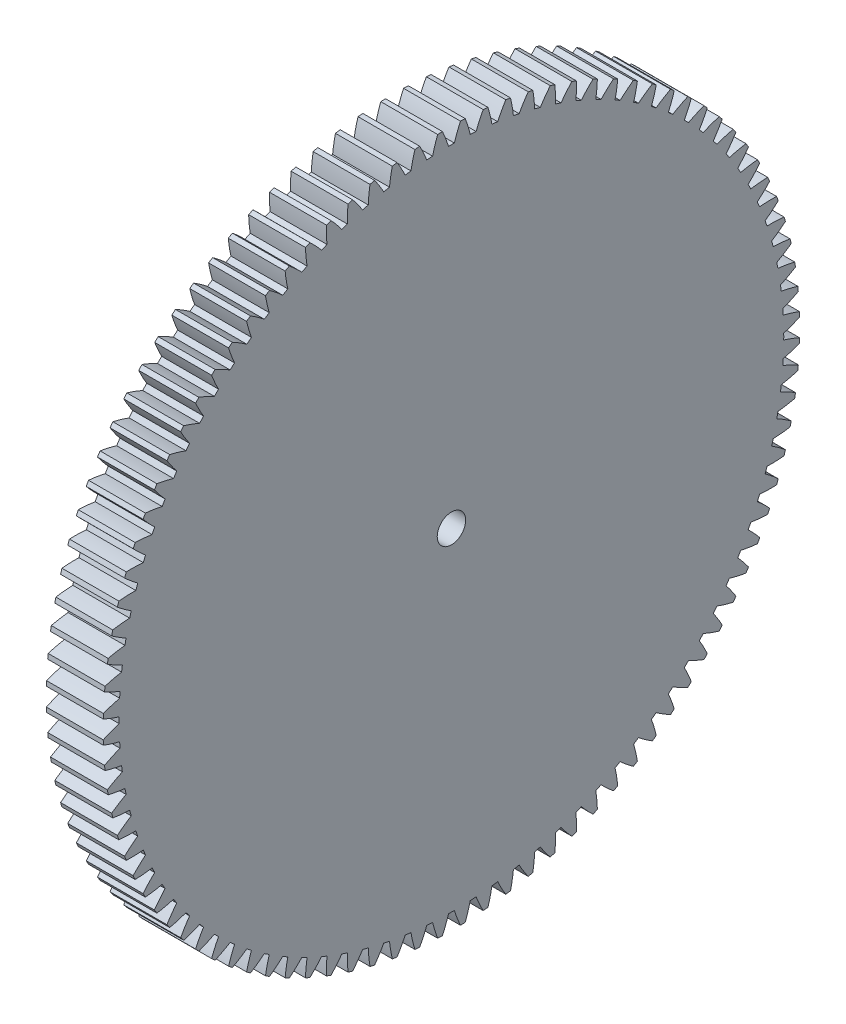
SolidWorks part; units mm, degrees
ref_plane "Plane1" through (0, 0, 0) normal (0, 0, 1) x (1, 0, 0)
ref_plane "Plane2" through (0, 0, 0) normal (0, 1, 0) x (1, 0, 0)
ref_plane "Plane3" through (0, 0, 0) normal (1, 0, 0) x (0, 0, -1)
sketch "HoldingSke" plane through (0, 0, 0) normal (0, 1, 0) x (1, 0, 0)
  line L0 (0, 0) -> (-0.0836, -0.7956)
  line L1 (-15, 0) -> (100, 0) construction
  line L2 (0, 0) -> (-2.1039, 2.3779)
  line L3 (0, 0) -> (-11.863, 4.5341)
  line L4 (0, 0) -> (-0.9027, 8.5887)
  line L5 (0, 0) -> (-46.8476, -17.4728)
  line L6 (0, 0) -> (-8.2896, -5.593)
  line L7 (-2.1039, 2.3779) -> (8.6586, 51.2059)
  line L8 (-76.2, 54.61) -> (-75.3, 54.61)
  line L9 (-71.009, 38.7566) -> (-53.1078, 45.2721)
  line L10 (-76.2, 71.12) -> (104.1128, 71.12)
  line L11 (0, 0) -> (-10, 0)
  line L12 (-76.2, 101.6) -> (-76.155, 101.6)
  line L13 (24.9733, 27.94) -> (52.9518, 28.4284)
  line L14 (24.9733, 27.94) -> (24.9743, 27.94)
  line L15 (24.9733, 27.94) -> (100.4006, 29.5858)
  line L16 (-63.627, -1.25) -> (-12.827, -1.25)
  circle A0 centre (0, 0) radius 2.5
  circle A1 centre (0, 0) radius 37.5
  circle A2 centre (0, 0) radius 37.5
  circle A3 centre (0, 0) radius 2.5
  dimension "MHD" = 75
  dimension "Hub_dia" = 75
  dimension "Bore" = 5
  dimension "MBD" = 5
  dimension "Num_teeth" = 96
  dimension "Pitch" = 0.8
  dimension "Overall_len" = 50
  dimension "Show_teeth" = 96
  dimension "Thickness" = 10
  dimension "OAL" = 50.0001
  dimension "T_dim" = 0.9
  dimension "Ap" = 20
  dimension "H" = 19.05
  dimension "Pitch_radius" = 180.3128
  dimension "Width" = 10
  dimension "Backlash" = 0.045
  dimension "Addendum_fac" = 1
  dimension "Dedendum_fac" = 1.25
  dimension "Clearance_fac" = 0.25
  dimension "Dedendum_add" = 0.001
  dimension "Module" = 1.25
sketch "BasProSke" plane through (0, 0, 0) normal (0, 1, 0) x (1, 0, 0)
  line L0 (-10, 0) -> (60, 0) construction
  line L1 (0, 0) -> (0, 61.25)
  line L2 (0, 0) -> (10, 0)
  line L3 (10, 0) -> (10, 61.25)
  line L4 (10, 61.25) -> (0, 61.25)
  dimension "Thickness" = 10
  dimension "Diameter" = 122.5
revolve "Base-Revolve" add sketch "BasProSke" angle 360 about L0
sketch "TooCutSke" plane through (0, 0, 0) normal (1, 0, 0) x (0, 0, -1)
  line L1 (0, 0) -> (0, 107) construction
  line L2 (0, 0) -> (-1.0605, 59.9906) construction
  line L3 (0, 0) -> (-3.9258, 119.9222) construction
  line L4 (-1.0605, 59.9906) -> (-1.9629, 59.9611) construction
  arc A0 (0.5154, 58.4342) -> (-0.5154, 58.4342) centre (0, 0) ccw
  arc A1 (1.5946, 61.2546) -> (-1.5946, 61.2546) centre (0, 0) ccw
  circle A2 centre (0, 0) radius 60 construction
  circle A3 centre (0, 0) radius 56.3816 construction
  arc A4 (-0.5154, 58.4342) -> (-1.5946, 61.2546) centre (-23.4257, 51.2846) ccw
  arc A5 (1.5946, 61.2546) -> (0.5154, 58.4342) centre (23.4257, 51.2846) ccw
  dimension "Root_dia" = 116.873
  dimension "Overcut_dia" = 122.5508
  dimension "Pitch_dia" = 120
  dimension "Base_dia" = 112.7631
  dimension "Flank_rad" = 24
  dimension "Half_ang" = 1.875
  dimension "Half_CT" = 0.903
extrude "ToothCut" cut sketch "TooCutSke" along normal through all
fillet "Breaks" [suppressed] radius 0.025
fillet "RootFillets" [suppressed] radius 0.3135
pattern_circular "TeethCuts" count 96 every 3.75 about axis through (-10, 0, 0) along (1, 0, 0) of "ToothCut", "RootFillets", "Breaks"
sketch "HubNeaOneSke" plane through (0, 0, 0) normal (-1, 0, 0) x (0, 0, 1)
  circle A0 centre (0, 0) radius 37.5
  dimension "Diameter" = 75
extrude "HubNearOne" [suppressed] add sketch "HubNeaOneSke" along normal blind 40.0001
sketch "HubNeaBotSke" plane through (0, 0, 0) normal (-1, 0, 0) x (0, 0, 1)
  circle A0 centre (0, 0) radius 37.5
  dimension "Diameter" = 75
extrude "HubNearBoth" [suppressed] add sketch "HubNeaBotSke" along normal blind 20
ref_plane "FarPln" through (10, 0, 0) normal (1, 0, 0) x (0, 0, -1)
sketch "HubFarSke" plane through (10, 0, 0) normal (1, 0, 0) x (0, 0, -1)
  circle A0 centre (0, 0) radius 37.5
  dimension "Diameter" = 75
extrude "HubFar" [suppressed] add sketch "HubFarSke" along normal blind 20
sketch "BorSke" plane through (0, 0, 0) normal (1, 0, 0) x (0, 0, -1)
  circle A0 centre (0, 0) radius 2.5
  dimension "Diameter" = 5
extrude "Bore" cut sketch "BorSke" along normal mid plane 100.0001
sketch "KeySke" plane through (0, 0, 0) normal (1, 0, 0) x (0, 0, -1)
  line L0 (-1, 0) -> (-1, 3.4)
  line L1 (-1, 3.4) -> (1, 3.4)
  line L2 (1, 3.4) -> (1, 0)
  line L3 (0, 0) -> (0, 34) construction
  line L4 (-1, 0) -> (1, 0)
  dimension "Offset" = 3.4
  dimension "Width" = 2
extrude "Keyway" [suppressed] cut sketch "KeySke" along normal mid plane 100.0001
pattern_circular "Keyway2" [suppressed] count 2 every 90 about axis through (-10, 0, 0) along (1, 0, 0)
equation "' \"Module@HoldingSke\" = 6.35"
equation "' \"Num_teeth@HoldingSke\" = 12"
equation "' \"Ap@HoldingSke\" =  20"
equation "' \"Ap@HoldingSke\" = 20"
equation "' \"Width@HoldingSke\" = 0.5 * 25.4"
equation "' \"Hub_dia@HoldingSke\"= 1 * 25.4"
equation "' \"Hub_dia@HoldingSke\" = 1 * 25.4"
equation "' \"Overall_len@HoldingSke\" = 1.0 * 25.4"
equation "' \"Bore@HoldingSke\" = 0.75 * 25.4"
equation "' \"T_dim@HoldingSke\" = 0.1 * 25.4"
equation "' \"Width@KeySke\" = 0.25 * 25.4"
equation "' \"Show_teeth@HoldingSke\" = 13"
equation "' \"Backlash@HoldingSke\" = 0.009 * 25.4"
equation "' \"Addendum_fac@HoldingSke\" = 1.0"
equation "' \"Dedendum_fac@HoldingSke\" = 1.25"
equation "' \"Dedendum_add@HoldingSke\" = 0.00005 * 25.4"
equation "' \"Clearance_fac@HoldingSke\" = 0.25"
equation "\"Pitch@HoldingSke\" = 1 / \"Module@HoldingSke\""
equation "\"Overcut_dia@TooCutSke\" = (\"Num_teeth@HoldingSke\" + 2 * \"Addendum_fac@HoldingSke\") / \"Pitch@HoldingSke\" + 0.002 * 25.4"
equation "\"Pitch_dia@TooCutSke\" = \"Num_teeth@HoldingSke\" / \"Pitch@HoldingSke\""
equation "\"Base_dia@TooCutSke\" = \"Num_teeth@HoldingSke\" / \"Pitch@HoldingSke\" * cos((\"Ap@HoldingSke\"  * 3.14159265 / 180))"
equation "\"Root_dia@TooCutSke\" = (\"Num_teeth@HoldingSke\" + 2) / \"Pitch@HoldingSke\" - 2 * (\"Addendum_fac@HoldingSke\" + \"Dedendum_fac@HoldingSke\") / \"Pitch@HoldingSke\" - \"Dedendum_add@HoldingSke\" * 2"
equation "\"Half_ang@TooCutSke\" = 180 / \"Num_teeth@HoldingSke\""
equation "\"Half_CT@TooCutSke\" = \"Num_teeth@HoldingSke\" / \"Pitch@HoldingSke\" * sin((3.14159265 / 2 / \"Num_teeth@HoldingSke\")) / 2 - 7 * \"Backlash@HoldingSke\" / 4"
equation "\"Flank_rad@TooCutSke\" = \"Num_teeth@HoldingSke\" / \"Pitch@HoldingSke\" / 5"
equation "\"Radius@RootFillets\" = \"Clearance_fac@HoldingSke\" / \"Pitch@HoldingSke\" + \"Dedendum_add@HoldingSke\""
equation "\"Break_rad@Breaks\" = 0.02 / \"Pitch@HoldingSke\""
equation "\"Thickness@HoldingSke\" = \"Width@HoldingSke\""
equation "\"OAL@HoldingSke\" = \"Thickness@HoldingSke\""
equation "\"MHD@HoldingSke\" = (\"Num_teeth@HoldingSke\" + 2) / \"Pitch@HoldingSke\" - 2 * (\"Addendum_fac@HoldingSke\" + \"Dedendum_fac@HoldingSke\")  / \"Pitch@HoldingSke\" - \"Dedendum_add@HoldingSke\" * 2"
equation "\"MBD@HoldingSke\" = (\"Num_teeth@HoldingSke\" + 2) / \"Pitch@HoldingSke\" - 2 * (\"Addendum_fac@HoldingSke\" + \"Dedendum_fac@HoldingSke\")  / \"Pitch@HoldingSke\" - \"Dedendum_add@HoldingSke\" * 2 - 0.002 * 25.4"
equation "\"MHD@HoldingSke\" = ((sgn( \"MHD@HoldingSke\" - \"Hub_dia@HoldingSke\" )-1)*( \"MHD@HoldingSke\" - \"Hub_dia@HoldingSke\" ))/-2+ \"Hub_dia@HoldingSke\""
equation "\"MBD@HoldingSke\" = ((sgn( \"MBD@HoldingSke\" - \"Bore@HoldingSke\" )-1)*( \"MBD@HoldingSke\" - \"Bore@HoldingSke\" ))/-2+ \"Bore@HoldingSke\""
equation "\"OAL@HoldingSke\" = ((sgn( \"OAL@HoldingSke\" - \"Overall_len@HoldingSke\" )+1)*( \"OAL@HoldingSke\" - \"Overall_len@HoldingSke\" ))/2 + \"Overall_len@HoldingSke\" + 0.000002 * 25.4"
equation "\"Num_teeth@TeethCuts\" = int( \"Show_teeth@HoldingSke\" ) + 1"
equation "\"Num_teeth@TeethCuts\" = ((sgn( \"Num_teeth@TeethCuts\" - \"Num_teeth@HoldingSke\" )-1)*( \"Num_teeth@TeethCuts\" - \"Num_teeth@HoldingSke\" ))/-2+ \"Num_teeth@HoldingSke\""
equation "\"Num_teeth@TeethCuts\" = ((sgn( \"Num_teeth@TeethCuts\" - 2.0)+1)*( \"Num_teeth@TeethCuts\" - 2.0))/2 +2.0"
equation "\"Angle@TeethCuts\" = 360.0 / \"Num_teeth@HoldingSke\""
equation "\"Diameter@BasProSke\" = (\"Num_teeth@HoldingSke\" + 2 * \"Addendum_fac@HoldingSke\") / \"Pitch@HoldingSke\""
equation "\"Thickness@BasProSke\"  = \"Thickness@HoldingSke\""
equation "' \"Fillet_rad@BasProSke\" =  \"Thickness@HoldingSke\" * 0.05"
equation "' \"Fillet_rad@BasProSke\" = \"Thickness@HoldingSke\" * 0.05"
equation "\"MHD@HoldingSke\" = ((sgn( \"MHD@HoldingSke\" - \"Root_dia@TooCutSke\" )-1)*( \"MHD@HoldingSke\" - \"Root_dia@TooCutSke\" ))/-2+ \"Root_dia@TooCutSke\""
equation "\"Diameter@HubNeaOneSke\" = \"MHD@HoldingSke\""
equation "\"Length@HubNearOne\" = \"OAL@HoldingSke\" - \"Thickness@BasProSke\""
equation "\"Diameter@HubNeaBotSke\" = \"MHD@HoldingSke\""
equation "\"Length@HubNearBoth\" = ( \"OAL@HoldingSke\" - \"Thickness@BasProSke\" ) / 2.0"
equation "\"Thickness@FarPln\" = \"Thickness@BasProSke\""
equation "\"Diameter@HubFarSke\" = \"MHD@HoldingSke\""
equation "\"Length@HubFar\" = ( \"OAL@HoldingSke\" - \"Thickness@BasProSke\" ) / 2.0"
equation "\"Diameter@BorSke\" = \"MBD@HoldingSke\""
equation "\"D1@Bore\" = \"OAL@HoldingSke\" * 2.0"
equation "\"D1@Keyway\" = \"OAL@HoldingSke\" * 2.0"
equation "\"Offset@KeySke\" = \"T_dim@HoldingSke\" + \"MBD@HoldingSke\" / 2.0"
